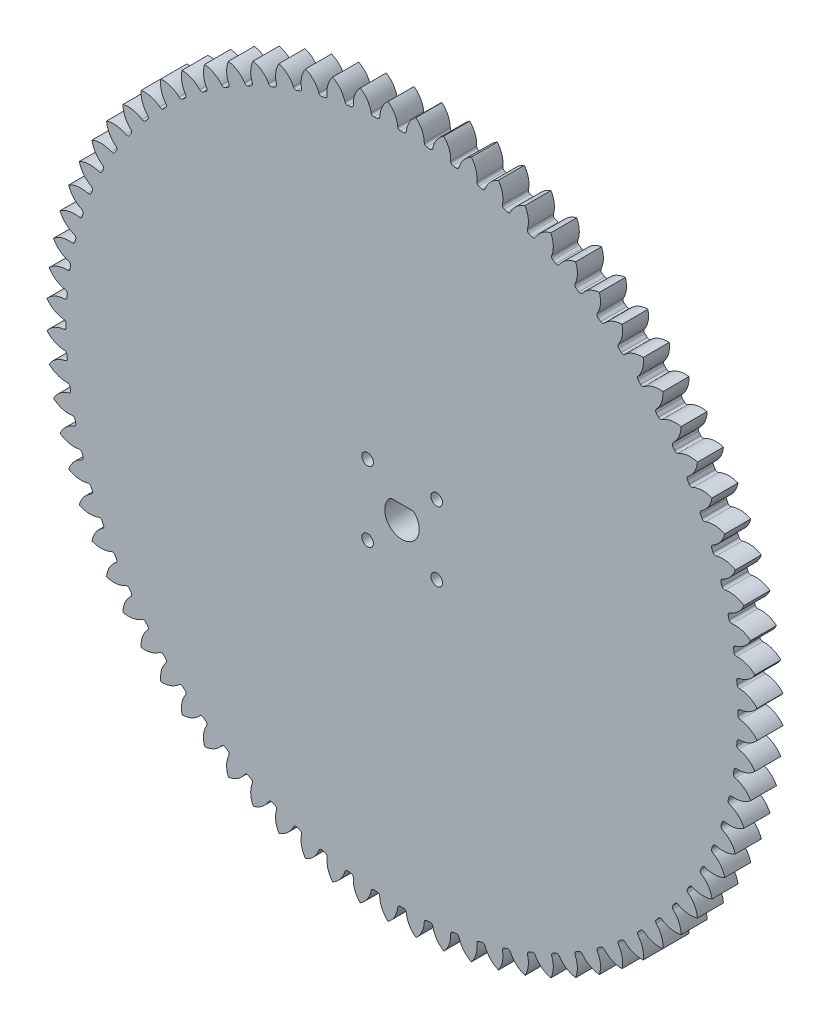
SolidWorks part; units mm, degrees
ref_plane "Front Plane" through (0, 0, 0) normal (0, 0, 1) x (1, 0, 0)
ref_plane "Top Plane" through (0, 0, 0) normal (0, 1, 0) x (1, 0, 0)
ref_plane "Right Plane" through (0, 0, 0) normal (1, 0, 0) x (0, 0, -1)
sketch "Sketch1" plane through (0, 0, 0) normal (0, 0, 1) x (1, 0, 0)
  circle A0 centre (0, 0) radius 120
  circle A1 centre (0, 0) radius 123
  dimension "D1" = 240
  dimension "D2" = 246
extrude "Boss-Extrude1" add sketch "Sketch1" along normal blind 9 contours A1 A0
sketch "Sketch2" plane through (0, 0, 9) normal (0, 0, 1) x (1, 0, 0)
  line L0 (0, 123) -> (0, 0) construction
  line L1 (0, 0) -> (9.6505, 122.6208) construction
  line L2 (0, 0) -> (4.829, 122.9052) construction
  line L3 (-1.4269, 116.2412) -> (0, 0) construction
  line L4 (-2.356, 119.9769) -> (2.356, 119.9769) construction
  line L5 (2.356, 119.9769) -> (7.0645, 119.7919) construction
  line L6 (-3.3685, 122.9539) -> (0, 113.6989) construction
  circle A0 centre (0, 0) radius 117 construction
  circle A2 centre (0, 0) radius 123 construction
  arc A3 (-4.856, 122.9041) -> (-1.4269, 116.2412) centre (-9.8145, 116.1383) cw
  circle A4 centre (0, 0) radius 123 construction
  arc A5 (4.856, 122.9041) -> (1.4269, 116.2412) centre (9.8145, 116.1383) ccw
  circle A6 centre (0, 0) radius 120 construction
  arc A7 (1.4269, 116.2412) -> (-1.4269, 116.2412) centre (0, 0) ccw
  circle M1 centre (0, 0) radius 123
  dimension "D1" = 4.5
  dimension "D2" = 6
  dimension "D4" = 20
  dimension "D3" = 0.75
extrude "Cut-Extrude1" cut sketch "Sketch2" against normal through all both and the other way through all contours A7 A5 A3 M1
fillet "Fillet1" radius 0.9 2 edges at (1.4269, 116.2412, 4.5) (-1.4269, 116.2412, 4.5)
pattern_circular "CirPattern3" count 80 over 360 about axis through (0, 0, 0) along (0, 0, 1) of "Fillet1", "Cut-Extrude1"
sketch "Sketch3" plane through (0, 0, 9) normal (0, 0, 1) x (1, 0, 0)
  point P6 (0, 5.975)
sketch "Sketch4" plane through (0, 0, 9) normal (0, 0, 1) x (1, 0, 0)
  line L0 (0, 0) -> (116.25, 0) construction
  line L1 (0, 0) -> (0.5769, 116.2486) construction
  line L2 (82.2012, 82.2012) -> (0, 0) construction
  arc A0 (116.2486, -0.5769) -> (116.2486, 0.5769) centre (0, 0) ccw construction
  circle A1 centre (0, 0) radius 116.25
  circle A2 centre (12.0208, 12.0208) radius 2
  circle A3 centre (-11.9009, 12.1395) radius 2
  circle A4 centre (-11.9009, -12.1395) radius 2
  circle A5 centre (12.0208, -12.0208) radius 2
  point P9 (82.2012, 82.2012)
  dimension "D3" = 4
  dimension "D1" = 45
  dimension "D2" = 17
extrude "Cut-Extrude3" cut sketch "Sketch4" against normal through all contours A3 | A5 | A4 | A2
sketch "Sketch5" plane through (0, 0, 9) normal (0, 0, 1) x (1, 0, 0)
  line L0 (-3.9592, 4.475) -> (3.9592, 4.475)
  arc A0 (-3.9592, 4.475) -> (3.9592, 4.475) centre (0, 0) ccw
  point P3 (0, 5.975)
  dimension "D1" = 11.95
  dimension "D2" = 1.5
extrude "Cut-Extrude4" cut sketch "Sketch5" against normal through all
fillet "Fillet2" radius 1 2 edges at (-3.9592, 4.475, 4.5) (3.9592, 4.475, 4.5)
equation "\"Module\"= 3mm"
equation "\"No. Teeth\"= 80"
equation "\"Contact Angle\"= 20"
equation "\"D1@Sketch1\"=\"Module\" * \"No. Teeth\""
equation "\"D2@Sketch1\"=(\"No. Teeth\" + 2) * \"Module\""
equation "\"D1@Sketch2\"=360/\"No. Teeth\""
equation "\"D2@Sketch2\"=2*\"Module\""
equation "\"D4@Sketch2\"=\"Contact Angle\""
equation "\"D1@Fillet1\"=0.3 * \"Module\""
equation "\"D1@CirPattern3\"=\"No. Teeth\""
